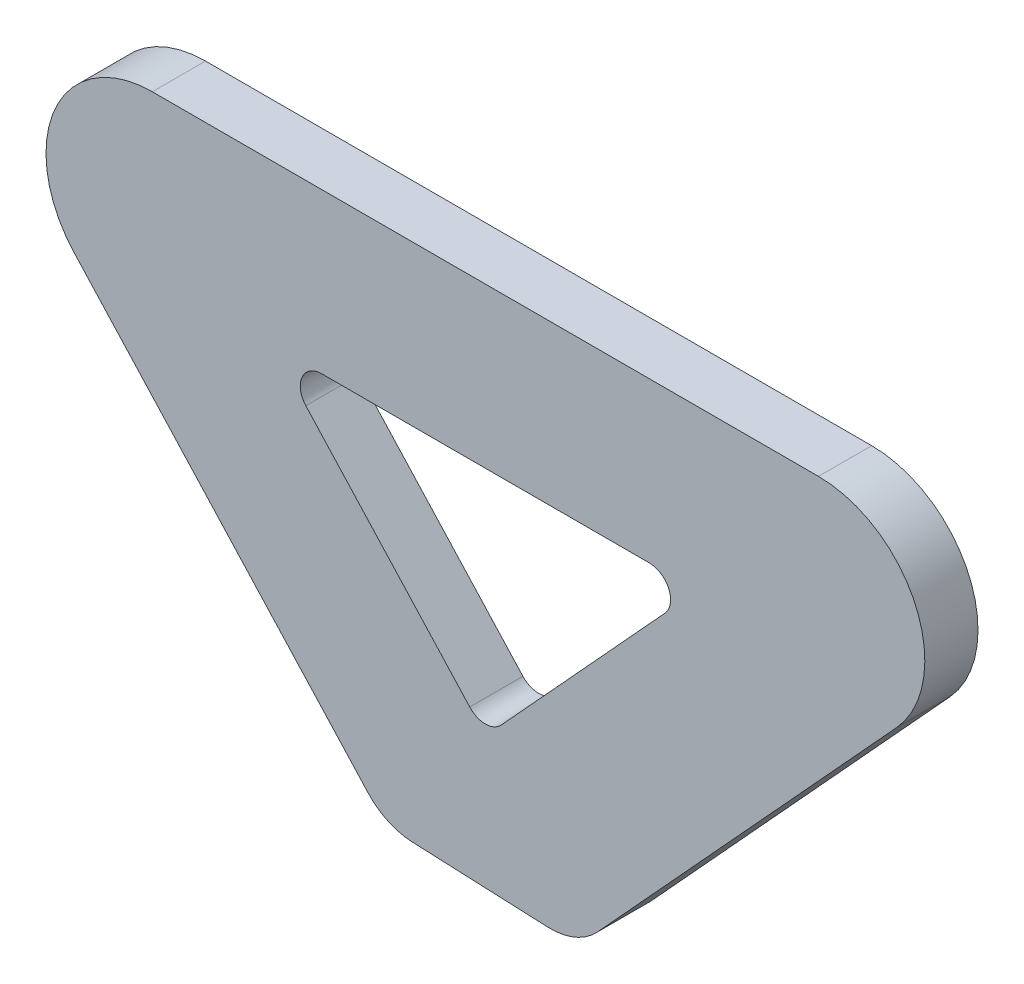
SolidWorks part; units mm, degrees
ref_plane "Front Plane" through (0, 0, 0) normal (0, 0, 1) x (1, 0, 0)
ref_plane "Top Plane" through (0, 0, 0) normal (0, 1, 0) x (1, 0, 0)
ref_plane "Right Plane" through (0, 0, 0) normal (1, 0, 0) x (0, 0, -1)
sketch "Sketch1" plane through (0, 0, 0) normal (0, 0, 1) x (1, 0, 0)
  line L1 (0, -74.9176) -> (-49.1364, -21.2786)
  line L2 (-39.7717, 0) -> (0, 0)
  line L11 (0, -46.7154) -> (25.3431, -19.05)
  line L12 (0, -74.9176) -> (0, 0) construction
  line L13 (0, -74.9176) -> (49.1364, -21.2786)
  line L17 (39.7717, 0) -> (0, 0)
  line L18 (25.3431, -19.05) -> (0, -19.05)
  line L22 (-25.3431, -19.05) -> (0, -19.05)
  line L23 (0, -46.7154) -> (-25.3431, -19.05)
  arc A0 (-49.1364, -21.2786) -> (-39.7717, 0) centre (-39.7717, -12.7) cw
  arc A5 (49.1364, -21.2786) -> (39.7717, 0) centre (39.7717, -12.7) ccw
  arc A6 (25.3431, -19.05) -> (25.3431, -19.05) centre (25.3431, -19.05) ccw
  arc A7 (-25.3431, -19.05) -> (-25.3431, -19.05) centre (-25.3431, -19.05) cw
  point P6 (-68.6288, 0)
  dimension "D4" = 12.7
  dimension "D1" = 101.6
  dimension "D2" = 68.6288
  dimension "D3" = 19.05
extrude "Boss-Extrude2" add sketch "Sketch1" along normal blind 6.35
chamfer "Chamfer1" distance 17.62 angle 45 1 edges at (0, -74.9176, 3.175)
fillet "Fillet1" radius 2.54 3 edges at (-25.3431, -19.05, 3.175) (0, -46.7154, 3.175) (25.3431, -19.05, 3.175)
fillet "Fillet2" radius 7.62 2 edges at (10.9835, -62.9276, 3.175) (-11.902, -61.925, 3.175)
